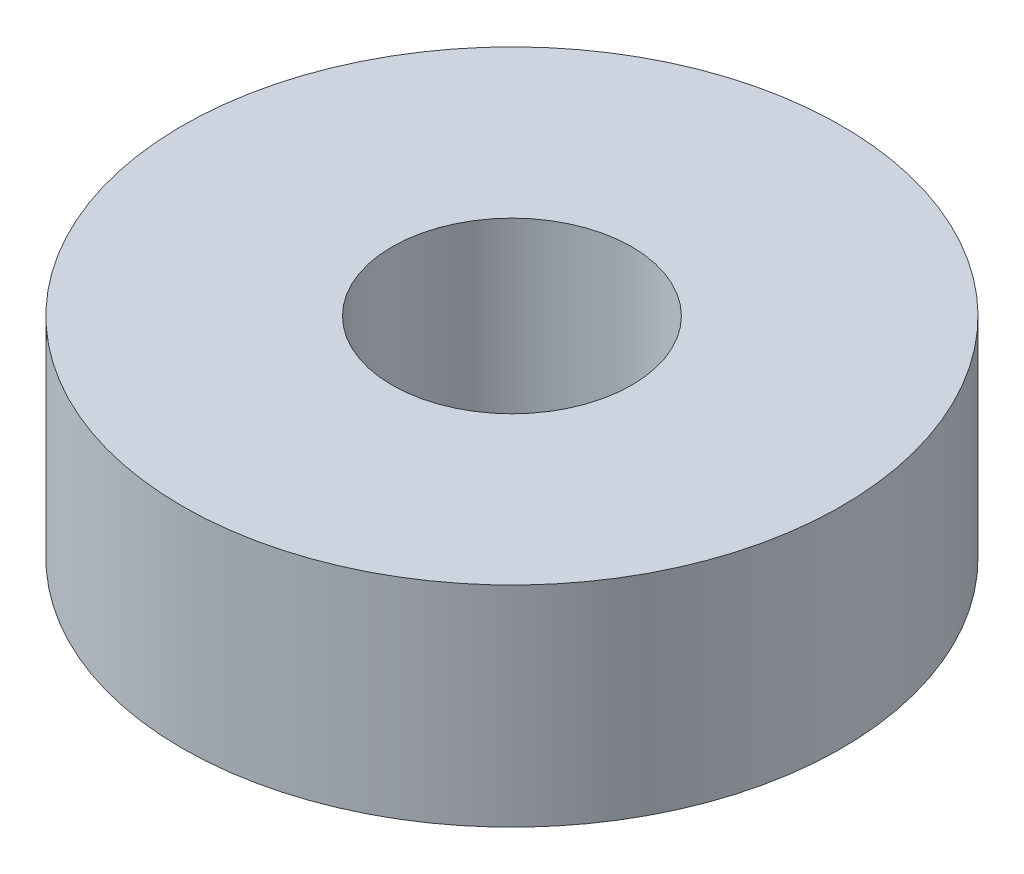
SolidWorks part; units mm, degrees
ref_plane "Front Plane" through (0, 0, 0) normal (0, 0, 1) x (1, 0, 0)
ref_plane "Top Plane" through (0, 0, 0) normal (0, 1, 0) x (1, 0, 0)
ref_plane "Right Plane" through (0, 0, 0) normal (1, 0, 0) x (0, 0, -1)
sketch "Sketch1" plane through (0, 0, 0) normal (0, 1, 0) x (1, 0, 0)
  circle A0 centre (0, 0) radius 4
  circle A1 centre (0, 0) radius 11
  dimension "D1" = 22
  dimension "D2" = 8
extrude "Boss-Extrude1" add sketch "Sketch1" along normal blind 7
